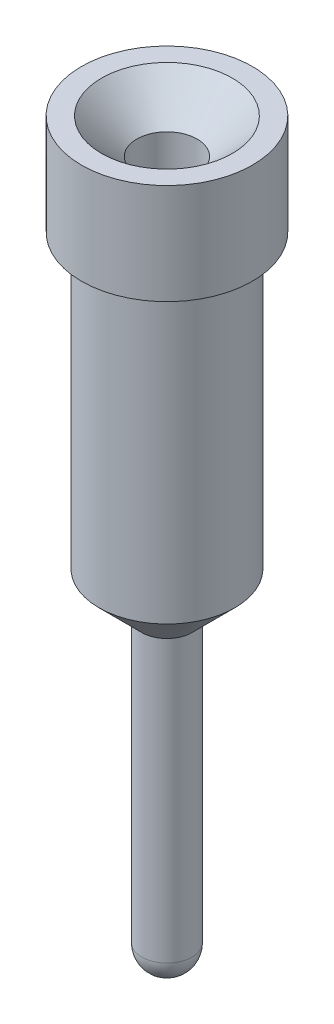
SolidWorks part; units mm, degrees
material "Beryllium Copper, UNS C17300"
ref_plane "Front Plane" through (0, 0, 0) normal (0, 0, 1) x (1, 0, 0)
ref_plane "Top Plane" through (0, 0, 0) normal (0, 1, 0) x (1, 0, 0)
ref_plane "Right Plane" through (0, 0, 0) normal (1, 0, 0) x (0, 0, -1)
sketch "Sketch1" plane through (0, 0, 0) normal (0, 0, 1) x (1, 0, 0)
  line L0 (0, 28.9926) -> (0, -77.4816) construction
  line L1 (0, -55) -> (0, 55) construction
  line L2 (-0.85, 0) -> (-0.85, -1)
  line L3 (55, 0) -> (-55, 0) construction
  line L4 (-0.85, -1) -> (-0.675, -1)
  line L5 (-0.675, -1) -> (-0.675, -3.9)
  line L6 (-0.675, -3.9) -> (-0.25, -4.325)
  line L7 (-0.25, -4.325) -> (-0.25, -7.12)
  line L8 (-0.85, 0) -> (-0.65, 0)
  line L9 (-0.3, -0.35) -> (-0.3, -3.7)
  line L10 (-0.3, -3.7) -> (0, -4)
  line L11 (0, -4) -> (0, -7.37)
  line L12 (-0.65, 0) -> (-0.3, -0.35)
  arc A0 (-0.25, -7.12) -> (0, -7.37) centre (0, -7.12) ccw
  point P16 (-0.3, 0)
  dimension "D1" = 45
  dimension "D2" = 1.7
  dimension "D3" = 1.35
  dimension "D4" = 1
  dimension "D5" = 3.9
  dimension "D6" = 0.5
  dimension "D7" = 3.7
  dimension "D8" = 0.6
  dimension "D9" = 7.12
revolve "Revolve1" add sketch "Sketch1" angle 360 about L0
